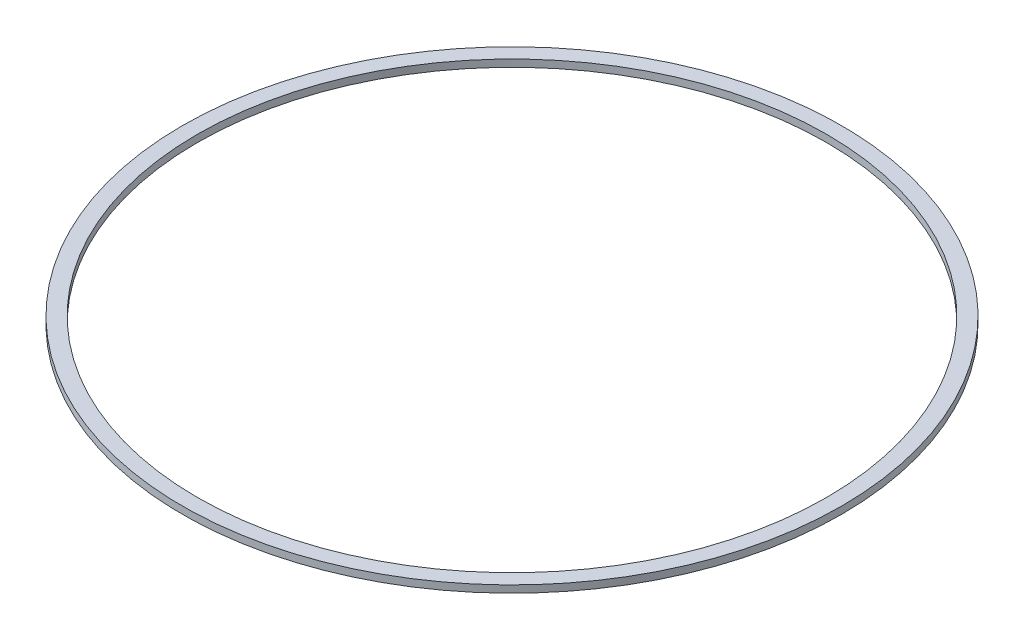
SolidWorks part; units mm, degrees
ref_plane "Front Plane" through (0, 0, 0) normal (0, 0, 1) x (1, 0, 0)
ref_plane "Top Plane" through (0, 0, 0) normal (0, 1, 0) x (1, 0, 0)
ref_plane "Right Plane" through (0, 0, 0) normal (1, 0, 0) x (0, 0, -1)
sketch "Sketch2" plane through (0, 0, 0) normal (0, 0, 1) x (1, 0, 0)
  line L1 (-55, 9.3) -> (-52.5, 9.3)
  line L2 (-55, 9.3) -> (-55, 8.1)
  line L3 (-55, 8.1) -> (-52.5, 8.1)
  line L4 (-52.5, 9.3) -> (-52.5, 8.1)
sketch "Sketch3" plane through (0, 0, 0) normal (0, 0, 1) x (1, 0, 0)
  line L0 (0, 0) -> (0, 30.013) construction
  line L4 (-52.5, 9.3) -> (-55, 9.3)
  line L5 (-52.5, 8.1) -> (-52.5, 9.3)
  line L6 (-55, 8.1) -> (-52.5, 8.1)
  line L7 (-55, 9.3) -> (-55, 8.1)
  line L8 (-52.5, 9.3) -> (-55, 9.3)
  line L9 (-52.5, 8.1) -> (-52.5, 9.3)
  line L10 (-55, 8.1) -> (-52.5, 8.1)
  line L11 (-55, 9.3) -> (-55, 8.1)
  dimension "D1" = 0
revolve "Revolve1" add sketch "Sketch3" angle 360 about L0
